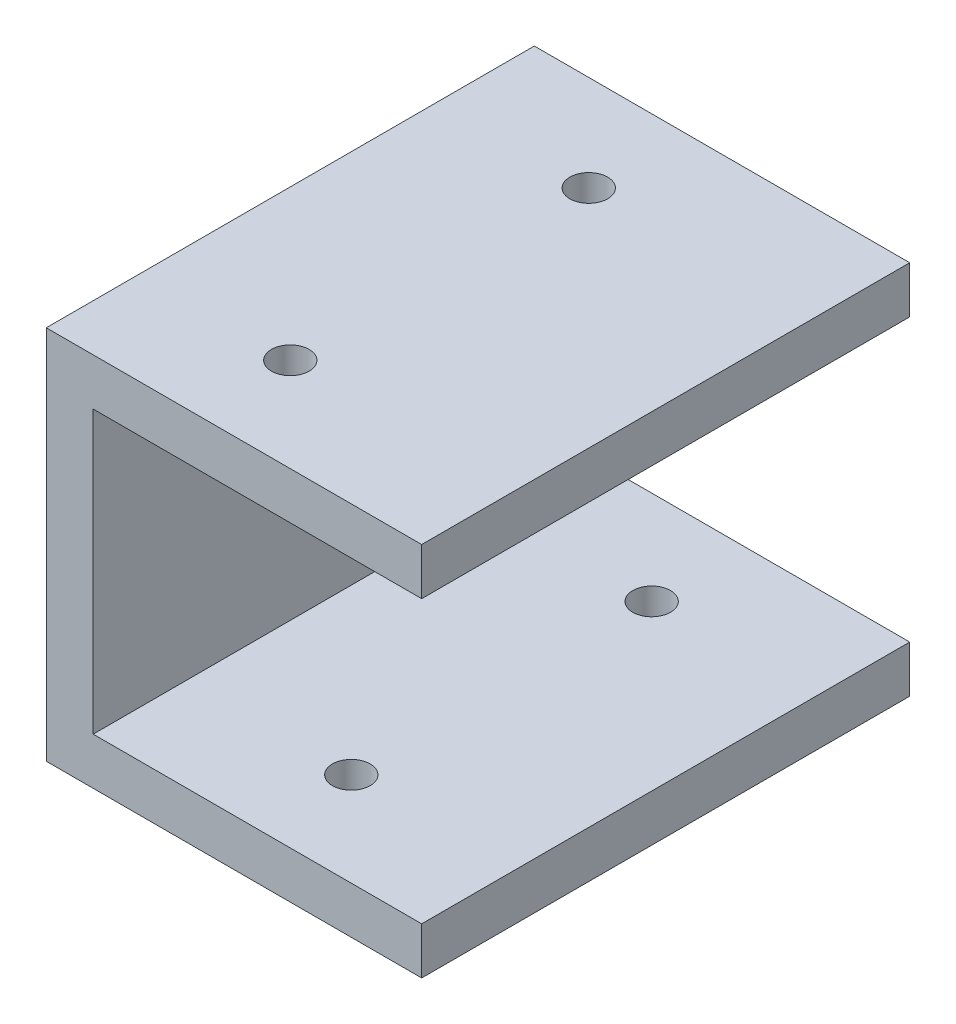
SolidWorks part; units mm, degrees
material "6063-T5"
ref_plane "Front Plane" through (0, 0, 0) normal (0, 0, 1) x (1, 0, 0)
ref_plane "Top Plane" through (0, 0, 0) normal (0, 1, 0) x (1, 0, 0)
ref_plane "Right Plane" through (0, 0, 0) normal (1, 0, 0) x (0, 0, -1)
sketch "Sketch1" plane through (0, 0, 0) normal (0, 0, 1) x (1, 0, 0)
  line L0 (-18.7358, -25.6169) -> (25.7142, -25.6169)
  line L1 (-25.0858, -19.2669) -> (25.7142, -19.2669)
  line L2 (-25.0858, -19.2669) -> (-25.0858, -70.0669)
  line L3 (-25.0858, -70.0669) -> (25.7142, -70.0669)
  line L4 (25.7142, -19.2669) -> (25.7142, -25.6169)
  line L6 (-18.7358, -63.7169) -> (25.7142, -63.7169)
  line L7 (-18.7358, -25.6169) -> (-18.7358, -63.7169)
  line L8 (19.3642, -25.6169) -> (19.3642, -63.7169) construction
  line L9 (-18.7358, -25.6169) -> (19.3642, -25.6169) construction
  line L10 (-18.7358, -63.7169) -> (19.3642, -63.7169) construction
  line L11 (25.7142, -63.7169) -> (25.7142, -70.0669)
  line L12 (25.7142, -19.2669) -> (25.7142, -70.0669) construction
  point P9 (0, 0)
  point P10 (19.3642, -25.6169)
  point P11 (19.3642, -25.6169)
  dimension "D1" = 50.8
  dimension "D2" = 50.8
  dimension "D3" = 6.35
extrude "Boss-Extrude1" add sketch "Sketch1" against normal blind 66.04
hole_wizard "1/4-20 Tapped Hole1" positions "Sketch2" profile "Sketch3" tap size "1/4-20" standard "ANSI Inch" end condition up to next
sketch "Sketch2" plane through (0, -19.2669, 0) normal (0, 1, 0) x (1, 0, 0)
  point P0 (-4.7658, 53.086)
  point P3 (-4.7658, 12.7)
sketch "Sketch3" plane through (-4.7658, -19.2669, -53.086) normal (1, 0, 0) x (0, 0, 1)
  line L0 (0, 0) -> (0, 6.35)
  line L1 (0, 6.35) -> (2.5527, 6.35)
  line L2 (2.5527, 6.35) -> (2.5527, 0)
  line L5 (2.5527, 0) -> (0, 0)
  line L11 (0, -6.35) -> (0, 107.95) construction
  dimension "Thread Major Dia." = 5.1054
  dimension "Thru Tap Drill Depth" = 6.35
hole_wizard "1/4-20 Tapped Hole2" positions "Sketch4" profile "Sketch5" tap size "1/4-20" standard "ANSI Inch" end condition up to next
sketch "Sketch4" plane through (0, -70.0669, 0) normal (0, -1, 0) x (-1, 0, 0)
  line L0 (-3.4892, 66.04) -> (-3.4892, 0) construction
  line L1 (25.0858, 66.04) -> (-25.7142, 66.04) construction
  line L2 (25.0858, 0) -> (-25.7142, 0) construction
  line L4 (-25.7142, 66.04) -> (-25.7142, 0) construction
  point P15 (-3.4892, 53.34)
  point P17 (-3.4892, 12.7)
  dimension "D1" = 22.225
  dimension "D2" = 12.7
  dimension "D3" = 12.7
sketch "Sketch5" plane through (3.4892, -70.0669, -12.7) normal (1, 0, 0) x (0, 0, -1)
  line L0 (0, 0) -> (0, 6.35)
  line L1 (0, 6.35) -> (2.5527, 6.35)
  line L2 (2.5527, 6.35) -> (2.5527, 0)
  line L5 (2.5527, 0) -> (0, 0)
  line L11 (0, -6.35) -> (0, 107.95) construction
  dimension "Thru Tap Drill Dia." = 5.1054
  dimension "Thru Tap Drill Depth" = 6.35
cosmetic thread "Hole Thread1"
cosmetic thread "Hole Thread2"
